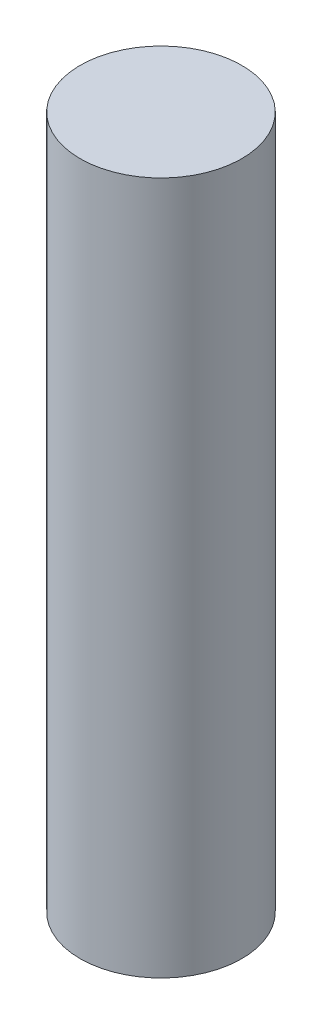
SolidWorks part; units mm, degrees
material "1060 Alloy"
ref_plane "Front Plane" through (0, 0, 0) normal (0, 0, 1) x (1, 0, 0)
ref_plane "Top Plane" through (0, 0, 0) normal (0, 1, 0) x (1, 0, 0)
ref_plane "Right Plane" through (0, 0, 0) normal (1, 0, 0) x (0, 0, -1)
sketch "Sketch1" plane through (0, 0, 0) normal (0, 1, 0) x (1, 0, 0)
  circle A0 centre (0, 0) radius 3.5
  dimension "D1" = 7
extrude "Boss-Extrude1" add sketch "Sketch1" along normal blind 30
sketch "Sketch2" plane through (0, 0, 0) normal (0, -1, 0) x (1, 0, 0)
  circle A0 centre (0, 0) radius 2.43
  dimension "D1" = 4.86
extrude "Cut-Extrude1" cut sketch "Sketch2" against normal blind 3
